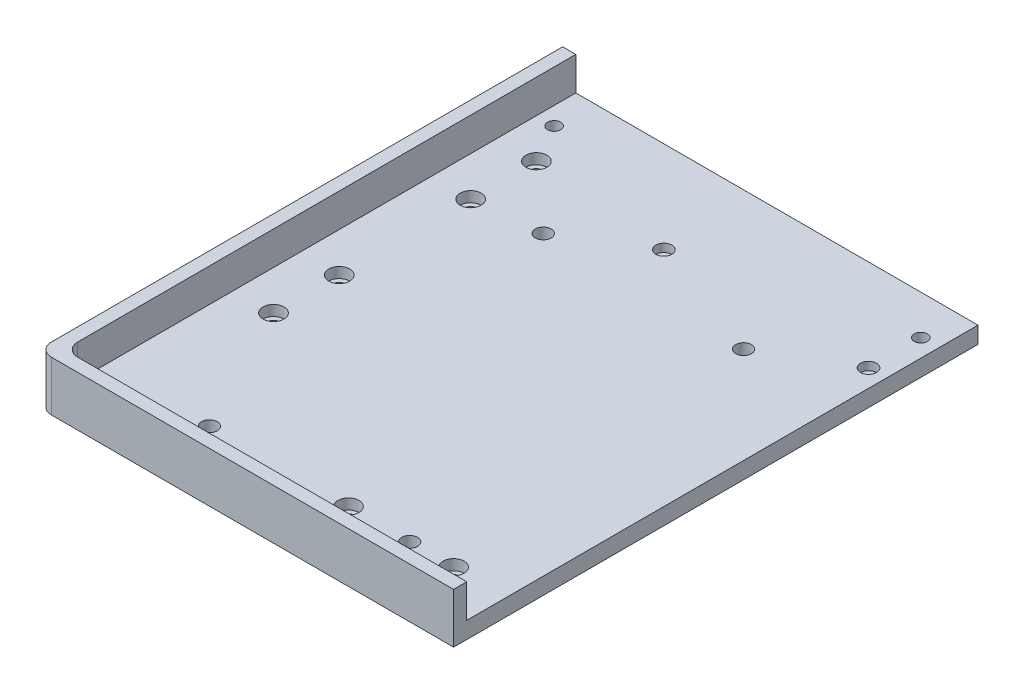
SolidWorks part; units mm, degrees
ref_plane "Front Plane" through (0, 0, 0) normal (0, 0, 1) x (1, 0, 0)
ref_plane "Top Plane" through (0, 0, 0) normal (0, 1, 0) x (1, 0, 0)
ref_plane "Right Plane" through (0, 0, 0) normal (1, 0, 0) x (0, 0, -1)
sketch "Sketch1" plane through (0, 0, 0) normal (0, 1, 0) x (1, 0, 0)
  line L1 (0, 0) -> (158, 0)
  line L2 (0, 0) -> (0, -199.5)
  line L3 (0, -199.5) -> (158, -199.5)
  line L4 (158, 0) -> (158, -199.5)
  dimension "D1" = 158
  dimension "D2" = 199.5
extrude "Boss-Extrude1" add sketch "Sketch1" along normal blind 6.35
sketch "Sketch2" [suppressed] plane through (0, 6.35, 0) normal (0, 1, 0) x (1, 0, 0)
  line L0 (0, -199.5) -> (158, -199.5) construction
  line L1 (81, -199.5) -> (0, -199.5)
  line L2 (81, -199.5) -> (81, -158.5)
  line L3 (81, -158.5) -> (0, -158.5)
  line L4 (0, -199.5) -> (0, -158.5)
  dimension "D1" = 81
  dimension "D2" = 41
sketch "Sketch3" plane through (0, 6.35, 0) normal (0, 1, 0) x (1, 0, 0)
  line L22 (0, 0) -> (0, -199.5) construction
  line L30 (0, -199.5) -> (158, -199.5) construction
  line L34 (0, 0) -> (0, -199.5)
  line L35 (0, -199.5) -> (158, -199.5)
  line L36 (5, 0) -> (5, -194.5)
  line L37 (5, -194.5) -> (158, -194.5)
  line L38 (158, -199.5) -> (158, -194.5)
  line L39 (0, 0) -> (5, 0)
  dimension "D1" = 5
extrude "Boss-Extrude2" add sketch "Sketch3" along normal blind 12.7
sketch "Sketch4" plane through (0, 6.35, 0) normal (0, -1, 0) x (1, 0, 0)
  line L0 (78, 179.5) -> (158, 179.5) construction
  line L3 (0, 199.5) -> (158, 199.5) construction
  line L4 (118, 179.5) -> (118, 188.5903) construction
  line L5 (20, 160) -> (20, 0) construction
  line L7 (158, 0) -> (0, 0) construction
  line L9 (20, 80) -> (152.6176, 80) construction
  line L10 (158, 199.5) -> (158, 0) construction
  line L12 (0, 0) -> (0, 199.5) construction
  point P8 (98, 179.5)
  point P11 (138, 179.5)
  point P20 (20, 130)
  point P21 (20, 105)
  point P22 (20, 30)
  point P23 (20, 80)
  point P24 (20, 55)
  dimension "D1" = 20
  dimension "D2" = 40
  dimension "D3" = 20
  dimension "D4" = 25
  dimension "D5" = 25
  dimension "D6" = 160
  dimension "D7" = 80
hole_wizard "CBORE for M4 SHCS1" positions "Sketch4" profile "Sketch5" counterbore size "M4" standard "ANSI Metric" end condition up to next
sketch "Sketch5" plane through (20, 6.35, 55) normal (1, 0, 0) x (0, 0, 1)
  line L0 (0, 0) -> (0, 6.35)
  line L1 (0, 6.35) -> (2.25, 6.35)
  line L3 (2.25, 6.35) -> (2.25, 4)
  line L4 (2.25, 4) -> (4, 4)
  line L5 (4, 4) -> (4, 0)
  line L7 (4, 0) -> (0, 0)
  line L11 (0, -6.35) -> (0, 107.95) construction
  dimension "Thru Hole Dia." = 4.5
  dimension "Thru Hole Depth" = 6.35
  dimension "C'Bore Dia." = 8
  dimension "C'Bore Depth" = 4
sketch "Sketch7" [suppressed] plane through (0, 0, 0) normal (0, 0, -1) x (-1, 0, 0)
  line L0 (-79, 19.05) -> (-79, 4.7647) construction
  line L2 (-158, 19.05) -> (0, 19.05) construction
  line L3 (-158, 19.05) -> (-29, 19.05)
  line L4 (-158, 19.05) -> (-158, 9.05)
  line L5 (-158, 9.05) -> (-29, 9.05)
  line L6 (-29, 19.05) -> (-29, 9.05)
  line L7 (0, 19.05) -> (0, 0) construction
  line L8 (-158, 6.35) -> (-158, 0) construction
  dimension "D1" = 29
  dimension "D2" = 10
extrude "Cut-Extrude2" [suppressed] cut sketch "Sketch7" against normal up to next
fillet "Fillet1" [suppressed] radius 5
fillet "Fillet2" radius 5 2 edges at (5, 12.7, 194.5) (0, 9.525, 199.5)
sketch "Sketch8" plane through (0, 6.35, 0) normal (0, 1, 0) x (1, 0, 0)
  line L1 (121.3, -179.5) -> (45.1, -179.5) construction
  line L2 (121.3, -179.5) -> (121.3, -52.5) construction
  line L3 (121.3, -52.5) -> (45.1, -52.5) construction
  line L4 (45.1, -179.5) -> (45.1, -52.5) construction
  line L5 (121.3, -179.5) -> (45.1, -52.5) construction
  line L6 (121.3, -52.5) -> (45.1, -179.5) construction
  line L7 (5, -189.5) -> (5, 0) construction
  line L8 (158, -194.5) -> (10, -194.5) construction
  circle A0 centre (45.1, -52.5) radius 3
  circle A1 centre (121.3, -52.5) radius 3
  circle A2 centre (121.3, -179.5) radius 3
  circle A3 centre (45.1, -179.5) radius 3
  point P0 (83.2, -116)
  dimension "D1" = 6
  dimension "D2" = 76.2
  dimension "D3" = 127
  dimension "D4" = 40.1
  dimension "D5" = 15
extrude "Enclosure Mount" cut sketch "Sketch8" against normal through all
sketch "Sketch9" plane through (0, 6.35, 0) normal (0, 1, 0) x (1, 0, 0)
  line L0 (11.75, -15) -> (151.25, -15) construction
  line L2 (158, 0) -> (5, 0) construction
  circle A0 centre (11.75, -15) radius 2.5
  circle A1 centre (151.25, -15) radius 2.5
  point P4 (81.5, 0)
  point P5 (81.5, -15)
  dimension "D1" = 5
  dimension "D2" = 139.5
  dimension "D4" = 15
extrude "Fuse Mount" cut sketch "Sketch9" against normal through all
sketch "Sketch10" plane through (0, 6.35, 0) normal (0, 1, 0) x (1, 0, 0)
  line L0 (158, 0) -> (5, 0) construction
  circle A0 centre (151.25, -34.9) radius 3.05
  circle A1 centre (73.375, -34.9) radius 3.05
  point P4 (151.25, -15)
  dimension "D2" = 6.1
  dimension "D1" = 34.9
  dimension "D3" = 77.875
extrude "Magnets" cut sketch "Sketch10" against normal blind 3.1
equation "\"D4@Sketch8\"=38.1+2"
equation "\"D5@Sketch8\"=12.7+2.3"
